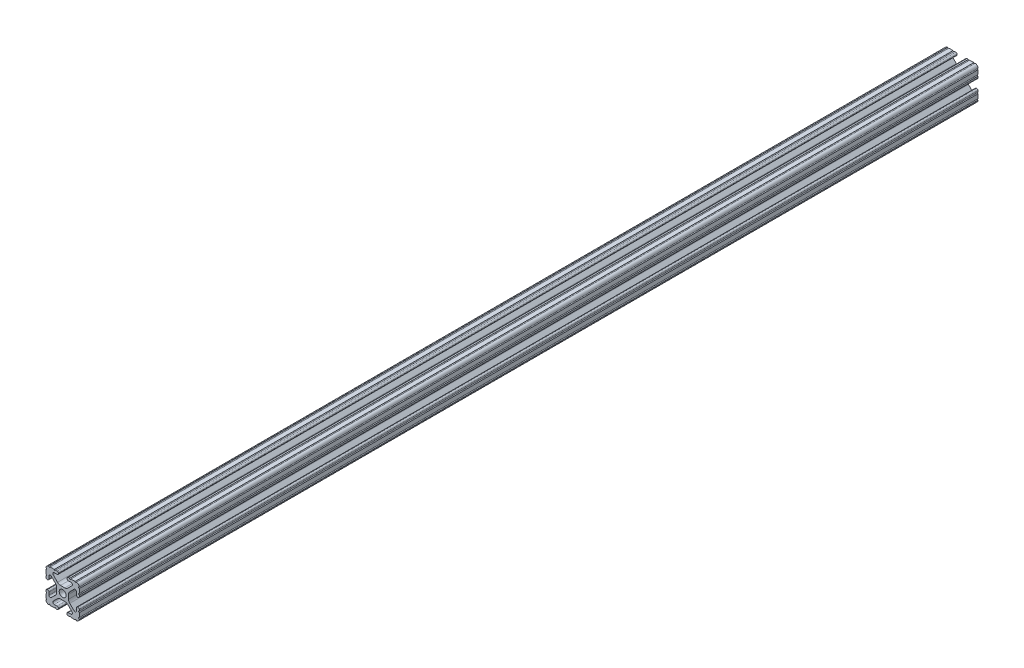
SolidWorks part; units mm, degrees
ref_plane "Front Plane" through (0, 0, 0) normal (0, 0, 1) x (1, 0, 0)
ref_plane "Top Plane" through (0, 0, 0) normal (0, 1, 0) x (1, 0, 0)
ref_plane "Right Plane" through (0, 0, 0) normal (1, 0, 0) x (0, 0, -1)
sketch "Sketch1" plane through (0, 0, 0) normal (0, 0, 1) x (1, 0, 0)
  line L88 (-7.1797, -8.6452) -> (-3.9523, -5.4237)
  line L89 (-1.7093, -4.4958) -> (1.7093, -4.4958)
  line L90 (3.9523, -5.4237) -> (7.1797, -8.6452)
  line L91 (6.4164, -10.4902) -> (4.2875, -10.4902)
  line L92 (3.2385, -11.5392) -> (3.2385, -11.651)
  line L93 (4.2875, -12.7) -> (5.3171, -12.7)
  line L94 (6.3331, -12.7) -> (9.5504, -12.7)
  line L95 (12.7, -9.5504) -> (12.7, -6.3331)
  line L96 (12.7, -5.3171) -> (12.7, -4.2875)
  line L97 (11.651, -3.2385) -> (11.5392, -3.2385)
  line L98 (10.4902, -4.2875) -> (10.4902, -6.4021)
  line L99 (8.7371, -7.1294) -> (5.441, -3.8408)
  line L100 (4.5085, -1.5932) -> (4.5085, 1.5932)
  line L101 (5.441, 3.8408) -> (8.7371, 7.1294)
  line L102 (10.4902, 6.4021) -> (10.4902, 4.2875)
  line L103 (11.5392, 3.2385) -> (11.651, 3.2385)
  line L104 (12.7, 4.2875) -> (12.7, 5.3171)
  line L105 (12.7, 6.3331) -> (12.7, 9.5504)
  line L106 (9.5504, 12.7) -> (6.3331, 12.7)
  line L107 (5.3171, 12.7) -> (4.2875, 12.7)
  line L108 (3.2385, 11.651) -> (3.2385, 11.5392)
  line L109 (4.2875, 10.4902) -> (6.4768, 10.4902)
  line L110 (7.207, 8.7244) -> (3.8983, 5.4232)
  line L111 (1.6558, 4.4958) -> (-1.6558, 4.4958)
  line L112 (-3.8983, 5.4232) -> (-7.207, 8.7244)
  line L113 (-6.4768, 10.4902) -> (-4.2875, 10.4902)
  line L114 (-3.2385, 11.5392) -> (-3.2385, 11.651)
  line L115 (-4.2875, 12.7) -> (-5.3171, 12.7)
  line L116 (-6.3331, 12.7) -> (-9.5504, 12.7)
  line L117 (-12.7, 9.5504) -> (-12.7, 6.3331)
  line L118 (-12.7, 5.3171) -> (-12.7, 4.2875)
  line L119 (-11.651, 3.2385) -> (-11.5392, 3.2385)
  line L120 (-10.4902, 4.2875) -> (-10.4902, 6.4021)
  line L121 (-8.7371, 7.1294) -> (-5.441, 3.8408)
  line L122 (-4.5085, 1.5932) -> (-4.5085, -1.5932)
  line L123 (-5.441, -3.8408) -> (-8.7371, -7.1294)
  line L124 (-10.4902, -6.4021) -> (-10.4902, -4.2875)
  line L125 (-11.5392, -3.2385) -> (-11.651, -3.2385)
  line L126 (-12.7, -4.2875) -> (-12.7, -5.3171)
  line L127 (-12.7, -6.3331) -> (-12.7, -9.5504)
  line L128 (-9.5504, -12.7) -> (-6.3331, -12.7)
  line L129 (-5.3171, -12.7) -> (-4.2875, -12.7)
  line L130 (-3.2385, -11.651) -> (-3.2385, -11.5392)
  line L131 (-4.2875, -10.4902) -> (-6.4164, -10.4902)
  circle A1 centre (0, 0) radius 2.6035
  arc A104 (-7.1797, -8.6452) -> (-6.4164, -10.4902) centre (-6.4164, -9.4098) ccw
  arc A105 (-1.7093, -4.4958) -> (-3.9523, -5.4237) centre (-1.7093, -7.6708) ccw
  arc A106 (3.9523, -5.4237) -> (1.7093, -4.4958) centre (1.7093, -7.6708) ccw
  arc A107 (6.4164, -10.4902) -> (7.1797, -8.6452) centre (6.4164, -9.4098) ccw
  arc A108 (4.2875, -10.4902) -> (3.2385, -11.5392) centre (4.2875, -11.5392) ccw
  arc A109 (3.2385, -11.651) -> (4.2875, -12.7) centre (4.2875, -11.651) ccw
  arc A110 (6.3331, -12.7) -> (5.3171, -12.7) centre (5.8251, -12.7) ccw
  arc A111 (10.5664, -12.6998) -> (9.5504, -12.7) centre (10.0584, -12.7) ccw
  arc A112 (10.5664, -12.6998) -> (12.6998, -10.5664) centre (10.5918, -10.5918) ccw
  arc A113 (12.7, -9.5504) -> (12.6998, -10.5664) centre (12.7, -10.0584) ccw
  arc A114 (12.7, -5.3171) -> (12.7, -6.3331) centre (12.7, -5.8251) ccw
  arc A115 (12.7, -4.2875) -> (11.651, -3.2385) centre (11.651, -4.2875) ccw
  arc A116 (11.5392, -3.2385) -> (10.4902, -4.2875) centre (11.5392, -4.2875) ccw
  arc A117 (8.7371, -7.1294) -> (10.4902, -6.4021) centre (9.4628, -6.4021) ccw
  arc A118 (4.5085, -1.5932) -> (5.441, -3.8408) centre (7.6835, -1.5932) ccw
  arc A119 (5.441, 3.8408) -> (4.5085, 1.5932) centre (7.6835, 1.5932) ccw
  arc A120 (10.4902, 6.4021) -> (8.7371, 7.1294) centre (9.4628, 6.4021) ccw
  arc A121 (10.4902, 4.2875) -> (11.5392, 3.2385) centre (11.5392, 4.2875) ccw
  arc A122 (11.651, 3.2385) -> (12.7, 4.2875) centre (11.651, 4.2875) ccw
  arc A123 (12.7, 6.3331) -> (12.7, 5.3171) centre (12.7, 5.8251) ccw
  arc A124 (12.6998, 10.5664) -> (12.7, 9.5504) centre (12.7, 10.0584) ccw
  arc A125 (12.6998, 10.5664) -> (10.5664, 12.6998) centre (10.5918, 10.5918) ccw
  arc A126 (9.5504, 12.7) -> (10.5664, 12.6998) centre (10.0584, 12.7) ccw
  arc A127 (5.3171, 12.7) -> (6.3331, 12.7) centre (5.8251, 12.7) ccw
  arc A128 (4.2875, 12.7) -> (3.2385, 11.651) centre (4.2875, 11.651) ccw
  arc A129 (3.2385, 11.5392) -> (4.2875, 10.4902) centre (4.2875, 11.5392) ccw
  arc A130 (7.207, 8.7244) -> (6.4768, 10.4902) centre (6.4768, 9.4563) ccw
  arc A131 (1.6558, 4.4958) -> (3.8983, 5.4232) centre (1.6558, 7.6708) ccw
  arc A132 (-3.8983, 5.4232) -> (-1.6558, 4.4958) centre (-1.6558, 7.6708) ccw
  arc A133 (-6.4768, 10.4902) -> (-7.207, 8.7244) centre (-6.4768, 9.4563) ccw
  arc A134 (-4.2875, 10.4902) -> (-3.2385, 11.5392) centre (-4.2875, 11.5392) ccw
  arc A135 (-3.2385, 11.651) -> (-4.2875, 12.7) centre (-4.2875, 11.651) ccw
  arc A136 (-6.3331, 12.7) -> (-5.3171, 12.7) centre (-5.8251, 12.7) ccw
  arc A137 (-10.5664, 12.6998) -> (-9.5504, 12.7) centre (-10.0584, 12.7) ccw
  arc A138 (-10.5664, 12.6998) -> (-12.6998, 10.5664) centre (-10.5918, 10.5918) ccw
  arc A139 (-12.7, 9.5504) -> (-12.6998, 10.5664) centre (-12.7, 10.0584) ccw
  arc A140 (-12.7, 5.3171) -> (-12.7, 6.3331) centre (-12.7, 5.8251) ccw
  arc A141 (-12.7, 4.2875) -> (-11.651, 3.2385) centre (-11.651, 4.2875) ccw
  arc A142 (-11.5392, 3.2385) -> (-10.4902, 4.2875) centre (-11.5392, 4.2875) ccw
  arc A143 (-8.7371, 7.1294) -> (-10.4902, 6.4021) centre (-9.4628, 6.4021) ccw
  arc A144 (-4.5085, 1.5932) -> (-5.441, 3.8408) centre (-7.6835, 1.5932) ccw
  arc A145 (-5.441, -3.8408) -> (-4.5085, -1.5932) centre (-7.6835, -1.5932) ccw
  arc A146 (-10.4902, -6.4021) -> (-8.7371, -7.1294) centre (-9.4628, -6.4021) ccw
  arc A147 (-10.4902, -4.2875) -> (-11.5392, -3.2385) centre (-11.5392, -4.2875) ccw
  arc A148 (-11.651, -3.2385) -> (-12.7, -4.2875) centre (-11.651, -4.2875) ccw
  arc A149 (-12.7, -6.3331) -> (-12.7, -5.3171) centre (-12.7, -5.8251) ccw
  arc A150 (-12.6998, -10.5664) -> (-12.7, -9.5504) centre (-12.7, -10.0584) ccw
  arc A151 (-12.6998, -10.5664) -> (-10.5664, -12.6998) centre (-10.5918, -10.5918) ccw
  arc A152 (-9.5504, -12.7) -> (-10.5664, -12.6998) centre (-10.0584, -12.7) ccw
  arc A153 (-5.3171, -12.7) -> (-6.3331, -12.7) centre (-5.8251, -12.7) ccw
  arc A154 (-4.2875, -12.7) -> (-3.2385, -11.651) centre (-4.2875, -11.651) ccw
  arc A155 (-3.2385, -11.5392) -> (-4.2875, -10.4902) centre (-4.2875, -11.5392) ccw
extrude "Boss-Extrude1" add sketch "Sketch1" along normal mid plane 685.8
sketch "Sketch2" plane through (4.5085, 0, 0) normal (1, 0, 0) x (0, 0, -1)
  line L0 (0, 0) -> (-393.7, 0) construction
  line L1 (-342.9, -1.5932) -> (-342.9, 1.5932) construction
  line L2 (0, 0) -> (0, 58.4486) construction
  line L3 (-342.9, 6.3331) -> (-342.9, 9.5504) construction
  circle A0 centre (-225.42, 0) radius 3.175
  circle A1 centre (225.42, 0) radius 3.175
  circle A2 centre (38.1, 0) radius 3.175
  circle A3 centre (-38.1, 0) radius 3.175
  dimension "D1" = 6.35
  dimension "D2" = 117.48
  dimension "D3" = 6.35
  dimension "D4" = 381
extrude "Cut-Extrude1" cut sketch "Sketch2" against normal through all both and the other way through all
